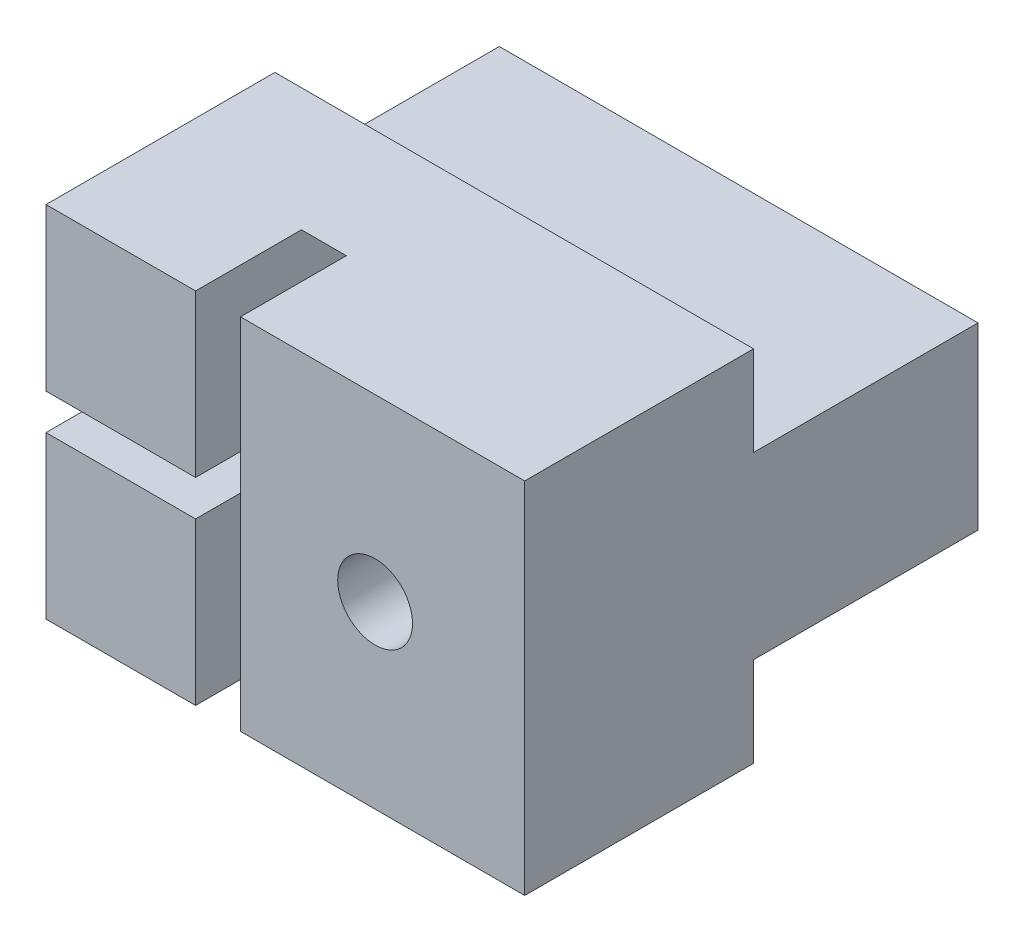
SolidWorks part; units mm, degrees
ref_plane "Спереди" through (0, 0, 0) normal (0, 0, 1) x (1, 0, 0)
ref_plane "Сверху" through (0, 0, 0) normal (0, 1, 0) x (1, 0, 0)
ref_plane "Справа" through (0, 0, 0) normal (1, 0, 0) x (0, 0, -1)
sketch "Эскиз1" plane through (0, 0, 0) normal (0, 0, 1) x (1, 0, 0)
  line L5 (-21.5997, 19) -> (-5.5997, 19)
  line L6 (-21.5997, 19) -> (-21.5997, 31)
  line L7 (-21.5997, 31) -> (-5.5997, 31)
  line L8 (-5.5997, 19) -> (-5.5997, 31)
  line L9 (-27.7383, 25) -> (-3.9171, 25) construction
  dimension "D1" = 12
  dimension "D2" = 16
extrude "Бобышка-Вытянуть1" add sketch "Эскиз1" along normal up to surface (7.65 mm away)
sketch "Эскиз2" plane through (0, 0, 7.65) normal (0, 0, 1) x (1, 0, 0)
  line L1 (-26.7383, 25) -> (-2.2483, 25) construction
  line L2 (-26.7383, 18) -> (-26.7383, 32) construction
  line L4 (-21.5997, 31) -> (-21.5997, 19) construction
  line L5 (-21.5997, 25.6) -> (-16.5997, 25.6)
  line L6 (-21.5997, 25.6) -> (-21.5997, 24.4)
  line L7 (-21.5997, 24.4) -> (-16.5997, 24.4)
  line L8 (-16.5997, 25.6) -> (-16.5997, 24.4)
  dimension "D1" = 1.2
  dimension "D2" = 5
extrude "Вырез-Вытянуть1" cut sketch "Эскиз2" against normal blind 4.5
sketch "Эскиз3" plane through (-16.5997, 0, 0) normal (-1, 0, 0) x (0, 0, 1)
  circle A0 centre (8, 25) radius 7.15
  dimension "D1" = 14.3
extrude "Вырез-Вытянуть2" cut sketch "Эскиз3" against normal blind 1.5
sketch "Эскиз4" plane through (0, 0, 0) normal (0, 0, -1) x (-1, 0, 0)
  line L0 (5.5997, 19) -> (5.5997, 31) construction
  line L1 (5.5997, 28) -> (21.5997, 28)
  line L2 (5.5997, 28) -> (5.5997, 22)
  line L3 (5.5997, 22) -> (21.5997, 22)
  line L4 (21.5997, 28) -> (21.5997, 22)
  line L5 (21.5997, 31) -> (21.5997, 19) construction
  line L6 (5.5997, 31) -> (21.5997, 31) construction
  dimension "D1" = 6
  dimension "D2" = 3
extrude "Бобышка-Вытянуть2" add sketch "Эскиз4" along normal blind 7.5
sketch "Эскиз5" plane through (0, 0, -7.5) normal (0, 0, -1) x (-1, 0, 0)
  line L0 (5.5997, 28) -> (5.5997, 22) construction
  line L2 (21.5997, 19) -> (5.5997, 19) construction
  circle A0 centre (10.5997, 25) radius 2.25
  dimension "D1" = 4.5
  dimension "D2" = 5
  dimension "D3" = 6
extrude "Вырез-Вытянуть3" cut sketch "Эскиз5" against normal up to surface (7.5 mm away) up to face at (-13.5997, 29.5, 0)
sketch "Эскиз6" plane through (0, 0, 0) normal (0, 0, -1) x (-1, 0, 0)
  circle A0 centre (10.5997, 25) radius 1.25
  dimension "D1" = 2.5
extrude "Вырез-Вытянуть4" cut sketch "Эскиз6" against normal through all
sketch "Эскиз7" plane through (0, 19, 0) normal (0, -1, 0) x (1, 0, 0)
  line L1 (-15.0997, 7.65) -> (-5.5997, 7.65)
  line L2 (-15.0997, 7.65) -> (-15.0997, 0)
  line L3 (-15.0997, 0) -> (-5.5997, 0)
  line L4 (-5.5997, 7.65) -> (-5.5997, 0)
extrude "Бобышка-Вытянуть3" [suppressed] add sketch "Эскиз7" along normal blind 9
sketch "Эскиз8" [suppressed] plane through (-5.5997, 0, 0) normal (1, 0, 0) x (0, 0, -1)
  line L0 (0, 10) -> (-7.65, 10) construction
  line L1 (-5.5, 10) -> (-9.5, 10)
  line L2 (-5.5, 10) -> (-5.5, 20)
  line L3 (-5.5, 20) -> (-9.5, 20)
  line L4 (-9.5, 10) -> (-9.5, 20)
  line L5 (0, 10) -> (0, 22) construction
  dimension "D1" = 10
  dimension "D2" = 4
  dimension "D3" = 5.5
extrude "Бобышка-Вытянуть4" [suppressed] add sketch "Эскиз8" along normal blind 10 and the other way up to vertex
sketch "Эскиз9" [suppressed] plane through (0, 0, 5.5) normal (0, 0, -1) x (-1, 0, 0)
  circle A0 centre (0.5997, 15) radius 2.75
  dimension "D1" = 5.5
extrude "Бобышка-Вытянуть5" [suppressed] add sketch "Эскиз9" along normal blind 5.5
